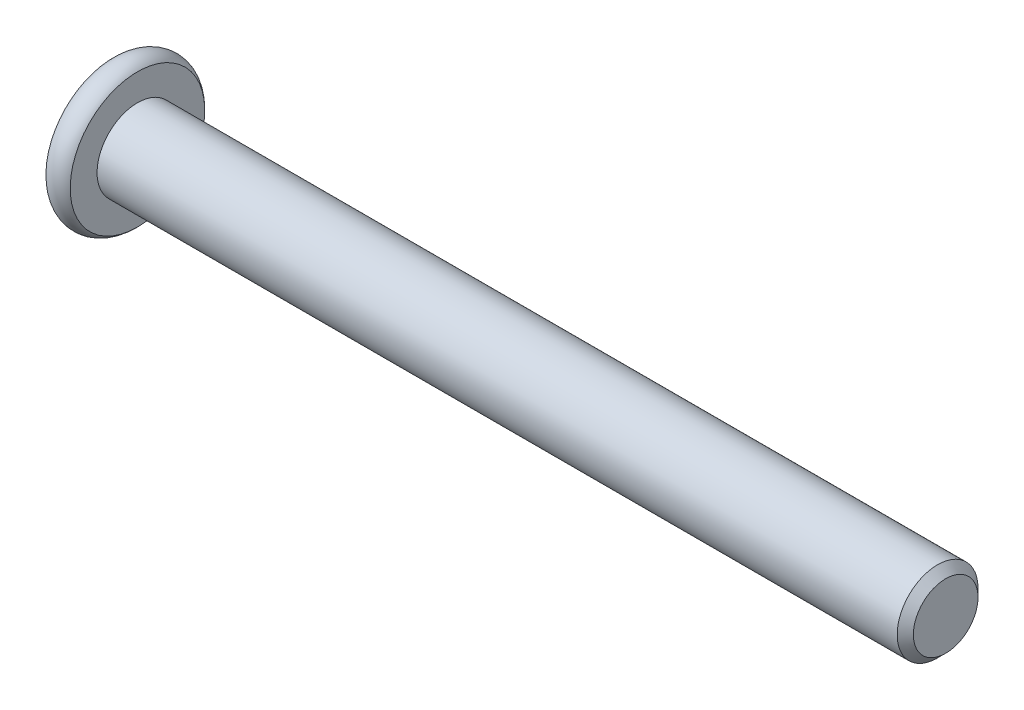
SolidWorks part; units mm, degrees
material "Plain Carbon Steel"
ref_plane "Front Plane" through (0, 0, 0) normal (0, 0, 1) x (1, 0, 0)
ref_plane "Top Plane" through (0, 0, 0) normal (0, 1, 0) x (1, 0, 0)
ref_plane "Right Plane" through (0, 0, 0) normal (1, 0, 0) x (0, 0, -1)
other "M5 x 15"
sketch "Sketch2" plane through (0, 0, 0) normal (1, 0, 0) x (0, 0, -1)
  circle A0 centre (0, 0) radius 2.5
  dimension "D1" = 5
extrude "Boss-Extrude1" add sketch "Sketch2" against normal blind 50
chamfer "Chamfer1" distance 0.5 angle 45 1 edges at (0, 0, -2.5)
sketch "Sketch6" plane through (0, 0, 0) normal (0, 0, 1) x (1, 0, 0)
  line L0 (-51.5, 0) -> (-51.5, 4.1614)
  line L1 (-51.5, 0) -> (-50, 0)
  line L2 (-50.75, 0) -> (-50.75, 3.5) construction
  line L6 (-50, 4.1614) -> (-50, 0)
  line L8 (-50, 0) -> (-14.6471, 0) construction
  line L10 (-50, 2.5) -> (-50, -2.5) construction
  arc A0 (-51.5, 4.1614) -> (-50, 4.1614) centre (-50.75, 3.5) cw
  dimension "D3" = 1
  dimension "D1" = 1.5
  dimension "D2" = 9
revolve "Revolve1" add sketch "Sketch6" angle 360 about L8
sketch "Sketch7" plane through (-51.5, 0, 0) normal (-1, 0, 0) x (0, 0, 1)
  line L1 (0, 1.7321) -> (-1.5, 0.866)
  line L2 (-1.5, 0.866) -> (-1.5, -0.866)
  line L3 (-1.5, -0.866) -> (0, -1.7321)
  line L4 (0, -1.7321) -> (1.5, -0.866)
  line L5 (1.5, -0.866) -> (1.5, 0.866)
  line L6 (1.5, 0.866) -> (0, 1.7321)
  circle A0 centre (0, 0) radius 1.5 construction
  dimension "D1" = 3
extrude "Cut-Extrude1" cut sketch "Sketch7" against normal blind 2.3
sketch "Sketch8" plane through (-51.5, 0, 0) normal (-1, 0, 0) x (0, 0, 1)
  circle A0 centre (0, 0) radius 1.7821
  dimension "D1" = 0.05
extrude "Cut-Extrude2" cut sketch "Sketch8" against normal blind 1 draft 45
